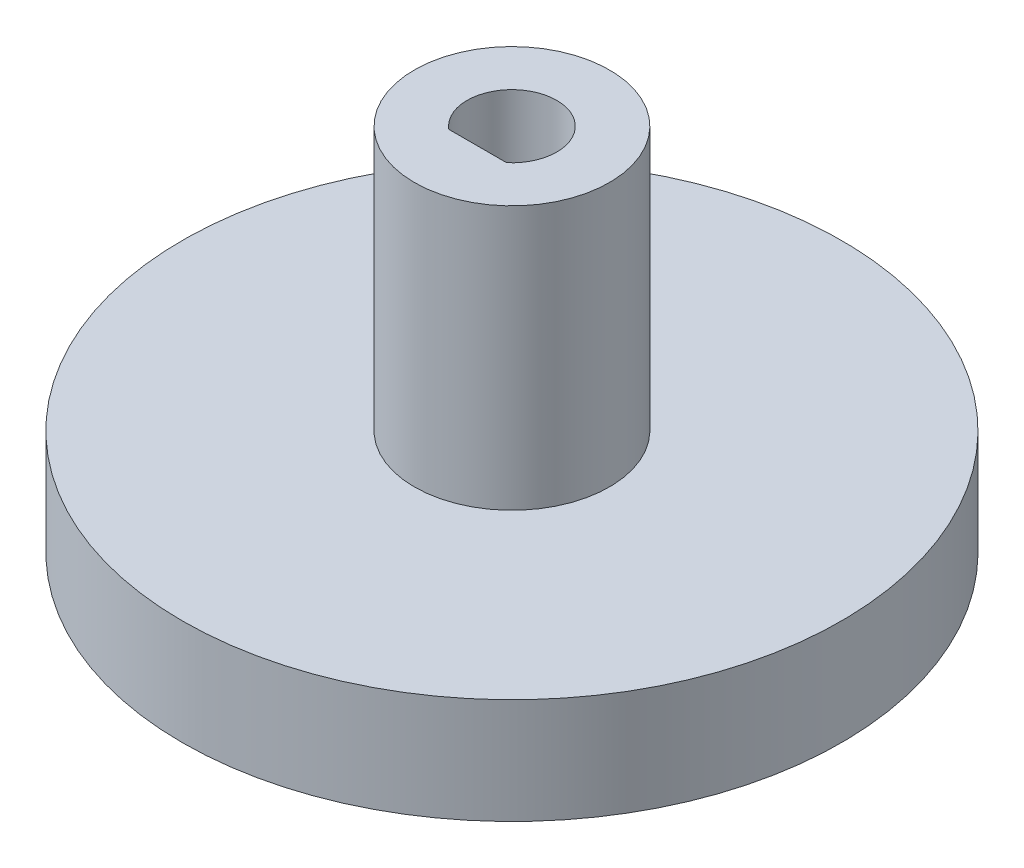
SolidWorks part; units mm, degrees
ref_plane "Front Plane" through (0, 0, 0) normal (0, 0, 1) x (1, 0, 0)
ref_plane "Top Plane" through (0, 0, 0) normal (0, 1, 0) x (1, 0, 0)
ref_plane "Right Plane" through (0, 0, 0) normal (1, 0, 0) x (0, 0, -1)
sketch "Sketch1" plane through (0, 0, 0) normal (0, 1, 0) x (1, 0, 0)
  line L0 (-1.0954, -1.3) -> (1.0954, -1.3)
  line L1 (0, -1.3) -> (0, -1.7)
  circle A0 centre (0, 0) radius 1.7
  circle A1 centre (0, 0) radius 12.5
  dimension "D1" = 3.4
  dimension "D2" = 25
  dimension "D3" = 0.4
extrude "Boss-Extrude1" add sketch "Sketch1" along normal blind 4 contours A1 A0 | L1 A0 L0 | L0 A0 L1
sketch "Sketch2" plane through (0, 4, 0) normal (0, 1, 0) x (1, 0, 0)
  line L1 (1.7, 0) -> (3.7, 0) construction
  line L2 (-1.0954, -1.3) -> (1.0954, -1.3)
  circle A0 centre (0, 0) radius 3.7
  arc A1 (1.0954, -1.3) -> (-1.0954, -1.3) centre (0, 0) ccw construction
  arc A2 (-1.0954, -1.3) -> (1.0954, -1.3) centre (0, 0) cw
  dimension "D2" = 1.7
  dimension "D1" = 2
extrude "Boss-Extrude2" add sketch "Sketch2" along normal blind 10
